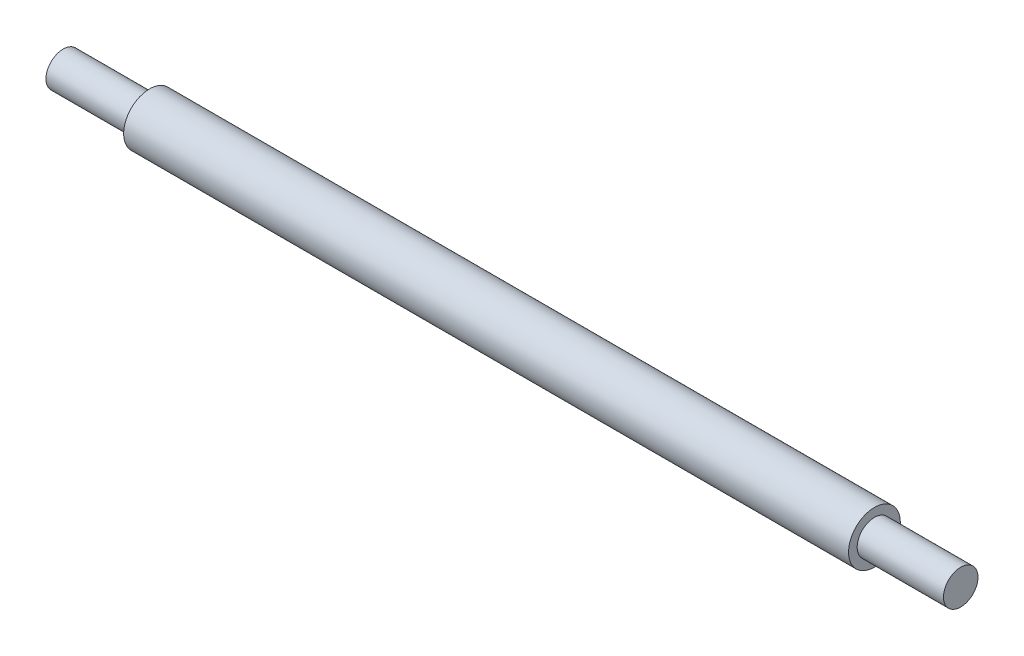
SolidWorks part; units mm, degrees
ref_plane "Front Plane" through (0, 0, 0) normal (0, 0, 1) x (1, 0, 0)
ref_plane "Top Plane" through (0, 0, 0) normal (0, 1, 0) x (1, 0, 0)
ref_plane "Right Plane" through (0, 0, 0) normal (1, 0, 0) x (0, 0, -1)
sketch "Sketch1" plane through (0, 0, 0) normal (0, 0, 1) x (1, 0, 0)
  line L0 (0, 0) -> (-40637.2456, 0) construction
  line L1 (0, 0) -> (0, 2)
  line L2 (0, 2) -> (10, 2)
  line L3 (10, 2) -> (10, 3)
  line L4 (10, 3) -> (94, 3)
  line L5 (94, 3) -> (94, 2)
  line L6 (94, 2) -> (104, 2)
  line L7 (104, 2) -> (104, 0)
  line L8 (0, 0) -> (104, 0)
  dimension "D1" = 104
  dimension "D2" = 10
  dimension "D3" = 10
  dimension "D4" = 6
  dimension "D5" = 4
revolve "Revolve1" add sketch "Sketch1" angle 360 about L0
